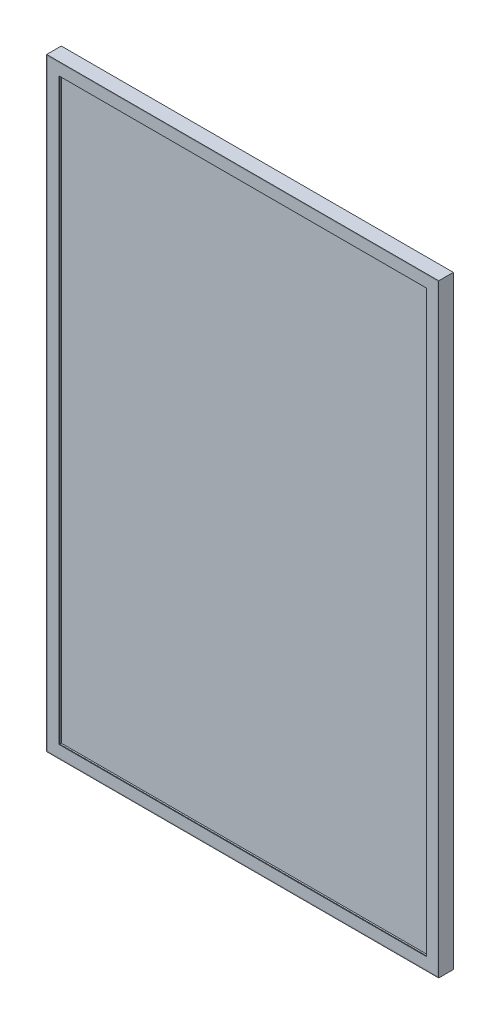
SolidWorks part; units mm, degrees
ref_plane "前视基准面" through (0, 0, 0) normal (0, 0, 1) x (1, 0, 0)
ref_plane "上视基准面" through (0, 0, 0) normal (0, 1, 0) x (1, 0, 0)
ref_plane "右视基准面" through (0, 0, 0) normal (1, 0, 0) x (0, 0, -1)
sketch "草图1" plane through (0, 0, 0) normal (0, 0, 1) x (1, 0, 0)
  line L1 (-268.5, 413.5) -> (268.5, 413.5)
  line L2 (-268.5, 413.5) -> (-268.5, -413.5)
  line L3 (-268.5, -413.5) -> (268.5, -413.5)
  line L4 (268.5, 413.5) -> (268.5, -413.5)
  line L5 (-268.5, 413.5) -> (268.5, -413.5) construction
  line L6 (-268.5, -413.5) -> (268.5, 413.5) construction
  point P0 (0, 0)
  dimension "D1" = 537
  dimension "D2" = 827
extrude "凸台-拉伸1" add sketch "草图1" along normal blind 20
shell "抽壳1" thickness 1
sketch "草图3" plane through (0, 0, 20) normal (0, 0, 1) x (1, 0, 0)
  line L0 (251.5, -396.5) -> (251.5, 396.5)
  line L1 (251.5, 396.5) -> (-251.5, 396.5)
  line L2 (-251.5, 396.5) -> (-251.5, -396.5)
  line L3 (-251.5, -396.5) -> (251.5, -396.5)
  line L4 (267.5, -412.5) -> (267.5, 412.5)
  line L5 (267.5, 412.5) -> (-267.5, 412.5)
  line L6 (-267.5, 412.5) -> (-267.5, -412.5)
  line L7 (-267.5, -412.5) -> (267.5, -412.5)
  line L8 (267.5, -412.5) -> (267.5, 412.5)
  line L9 (267.5, 412.5) -> (-267.5, 412.5)
  line L10 (-267.5, 412.5) -> (-267.5, -412.5)
  line L11 (-267.5, -412.5) -> (267.5, -412.5)
  dimension "D1" = 0
  dimension "D2" = 16
extrude "凸台-拉伸2" add sketch "草图3" against normal blind 1 separate body
